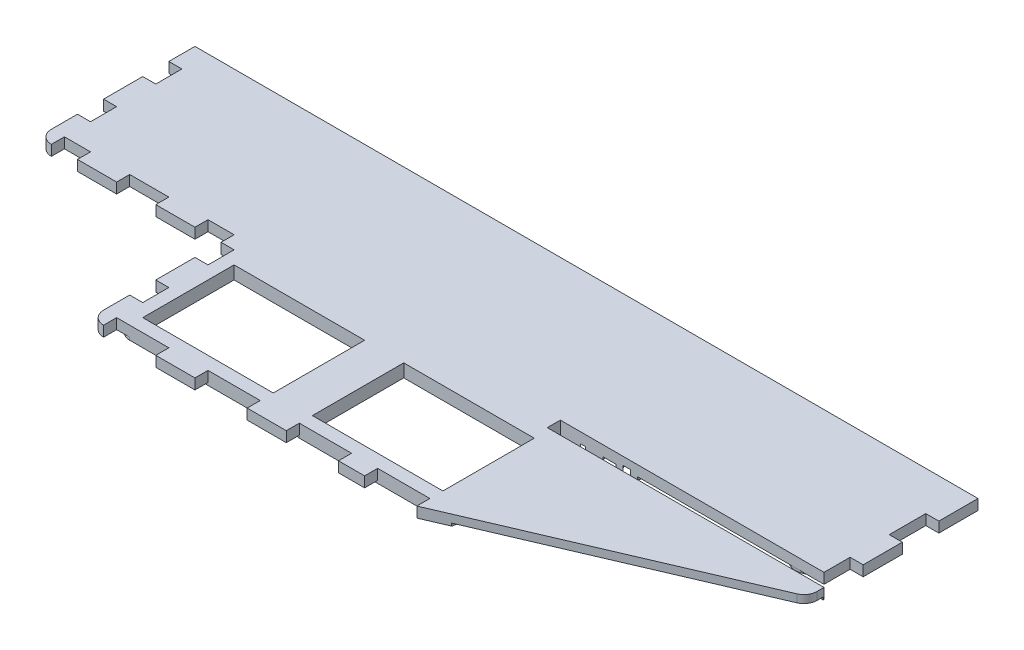
SolidWorks part; units mm, degrees
ref_plane "Front Plane" through (0, 0, 0) normal (0, 0, 1) x (1, 0, 0)
ref_plane "Top Plane" through (0, 0, 0) normal (0, 1, 0) x (1, 0, 0)
ref_plane "Right Plane" through (0, 0, 0) normal (1, 0, 0) x (0, 0, -1)
sketch "Sketch1" plane through (0, 0, 0) normal (0, 0, 1) x (1, 0, 0)
  line L0 (0, 0) -> (0, 254) construction
  line L1 (-381, 0) -> (0, 0)
  line L3 (-381, 6.35) -> (0, 6.35)
  line L4 (0, 0) -> (0, 6.35)
  line L5 (-381, 0) -> (-381, 6.35)
extrude "Boss-Extrude1" add sketch "Sketch1" along normal blind 139.7
sketch "Sketch2" plane through (0, 0, 0) normal (0, -1, 0) x (1, 0, 0)
  line L1 (-406.4, 139.7) -> (-406.4, 0) construction
  line L2 (-374.65, 76.2) -> (-292.1, 76.2)
  line L3 (-292.1, 76.2) -> (-292.1, 133.35)
  line L4 (-381, 139.7) -> (0, 139.7) construction
  line L5 (-285.75, 139.7) -> (-133.35, 139.7)
  line L6 (-133.35, 139.7) -> (-3.8486, 84.1994)
  line L7 (0, 139.7) -> (0, 0) construction
  line L8 (0, 78.3628) -> (0, 0)
  line L9 (0, 0) -> (-381, 0)
  line L10 (-381, 69.85) -> (-381, 0)
  line L11 (-381, 139.7) -> (-381, 0) construction
  arc A0 (-3.8486, 84.1994) -> (0, 78.3628) centre (-6.35, 78.3628) cw
  arc A1 (-292.1, 133.35) -> (-285.75, 139.7) centre (-285.75, 133.35) cw
  arc A3 (-381, 69.85) -> (-374.65, 76.2) centre (-374.65, 69.85) cw
  point P17 (0, 82.55)
  point P20 (-292.1, 139.7)
  point P21 (-381, 76.2)
  point P23 (-406.4, 76.2)
  dimension "D5" = 6.35
  dimension "D1" = 6.35
  dimension "D2" = 114.3
  dimension "D3" = 158.75
  dimension "D4" = 82.55
extrude "Cut-Extrude1" cut sketch "Sketch2" against normal through all
sketch "Sketch3" plane through (0, 6.35, 0) normal (0, 1, 0) x (1, 0, 0)
  line L0 (-133.35, -139.7) -> (-285.75, -139.7) construction
  line L1 (-279.4, -127) -> (-215.9, -127)
  line L2 (-279.4, -127) -> (-279.4, -82.55)
  line L3 (-279.4, -82.55) -> (-215.9, -82.55)
  line L4 (-215.9, -127) -> (-215.9, -82.55)
  line L5 (-196.85, -127) -> (-133.35, -127)
  line L6 (-196.85, -127) -> (-196.85, -82.55)
  line L7 (-196.85, -82.55) -> (-133.35, -82.55)
  line L8 (-133.35, -127) -> (-133.35, -82.55)
  line L9 (-292.1, -76.2) -> (-292.1, -133.35) construction
  dimension "D1" = 44.45
  dimension "D2" = 12.7
  dimension "D3" = 12.7
  dimension "D4" = 63.5
  dimension "D5" = 19.05
  dimension "D6" = 44.45
  dimension "D7" = 12.7
  dimension "D8" = 63.5
extrude "Cut-Extrude2" cut sketch "Sketch3" against normal through all contours L5 L8 L7 L6 | L1 L4 L3 L2
sketch "Sketch4" plane through (0, 0, 0) normal (0, -1, 0) x (1, 0, 0)
  line L0 (-285.75, 139.7) -> (-133.35, 139.7) construction
  line L1 (-279.4, 133.35) -> (-215.9, 133.35)
  line L2 (-285.75, 127) -> (-285.75, 25.4)
  line L3 (-279.4, 19.05) -> (-215.9, 19.05)
  line L4 (-209.55, 127) -> (-209.55, 25.4)
  line L5 (-127, 133.35) -> (-196.85, 133.35)
  line L7 (-131.8807, 19.05) -> (-196.85, 19.05)
  line L8 (-203.2, 127) -> (-203.2, 25.4)
  line L9 (-292.1, 76.2) -> (-292.1, 133.35) construction
  line L11 (-381, 0) -> (0, 0) construction
  line L12 (-215.9, 127) -> (-215.9, 82.55) construction
  line L13 (-127, 133.35) -> (-112.1376, 74.8789)
  line L14 (-112.1376, 74.8789) -> (-125.7444, 23.7664)
  arc A0 (-196.85, 133.35) -> (-203.2, 127) centre (-196.85, 127) ccw
  arc A1 (-215.9, 133.35) -> (-209.55, 127) centre (-215.9, 127) cw
  arc A2 (-279.4, 133.35) -> (-285.75, 127) centre (-279.4, 127) ccw
  arc A3 (-285.75, 25.4) -> (-279.4, 19.05) centre (-279.4, 25.4) ccw
  arc A4 (-215.9, 19.05) -> (-209.55, 25.4) centre (-215.9, 25.4) ccw
  arc A5 (-196.85, 19.05) -> (-203.2, 25.4) centre (-196.85, 25.4) cw
  arc A6 (-131.8807, 19.05) -> (-125.7444, 23.7664) centre (-131.8807, 25.4) ccw
  dimension "D3" = 6.35
  dimension "D1" = 6.35
  dimension "D2" = 6.35
  dimension "D4" = 6.35
  dimension "D5" = 19.05
  dimension "D6" = 6.35
  dimension "D7" = 6.35
  dimension "D8" = 19.05
extrude "Cut-Extrude3" cut sketch "Sketch4" against normal blind 1.27
sketch "Sketch5" plane through (0, 0, 0) normal (0, -1, 0) x (1, 0, 0)
  line L0 (-250.8616, 56.914) -> (-269.3149, 71.6766)
  line L1 (-248.4216, 50.9666) -> (-248.4331, 50.9773) construction
  line L3 (-267.7282, 76.2) -> (-229.317, 76.2)
  line L4 (-257.258, 53.8991) -> (-275.2733, 68.3113)
  line L5 (-184.3234, 76.2) -> (-133.6398, 76.2)
  line L6 (-196.85, 82.55) -> (-133.35, 82.55) construction
  line L9 (-142.8427, 29.9409) -> (-159.4602, 42.9343)
  line L10 (-227.2884, 29.9234) -> (-246.082, 44.9583)
  line L12 (-131.9836, 71.533) -> (-158.9921, 53.9033)
  line L15 (-124.9851, 68.5182) -> (-151.5288, 51.1918)
  line L21 (-220.0267, 32.246) -> (-239.6856, 47.9731)
  line L24 (-275.269, 33.4756) -> (-257.2515, 47.954)
  line L26 (-131.8807, 25.4) -> (-118.6989, 74.9159)
  line L28 (-131.8807, 25.4) -> (-118.6989, 74.9159)
  line L30 (-118.6989, 74.9159) -> (-131.9379, 127)
  line L37 (-269.5564, 29.9199) -> (-250.8486, 44.9531)
  line L38 (-215.9, 34.2294) -> (-215.9, 67.7374)
  line L40 (-248.5328, 50.9091) -> (-248.3486, 51.0351) construction
  line L41 (-246.095, 56.9191) -> (-227.7259, 71.6801)
  line L42 (-248.5328, 50.9091) -> (-248.5037, 50.8894) construction
  line L43 (-228.8751, 25.4) -> (-267.9653, 25.4)
  line L44 (-248.3486, 51.0351) -> (-248.5037, 50.8894) construction
  line L45 (-279.4, 66.3279) -> (-279.4, 35.4556)
  line L46 (-239.6921, 53.9182) -> (-220.031, 69.7173)
  line L47 (-133.6398, 76.2) -> (-133.372, 76.2)
  line L51 (-134.0223, 31.1049) -> (-151.793, 45)
  line L55 (-163.4215, 54.0923) -> (-185.888, 71.6591)
  line L57 (-164.1074, 50.5642) -> (-164.3654, 50.8) construction
  line L58 (-131.9379, 127) -> (-196.85, 127)
  line L59 (-171.3529, 45.8348) -> (-192.9216, 31.7558)
  line L60 (-164.3654, 50.8) -> (-164.0586, 50.5961) construction
  line L61 (-196.85, 127) -> (-196.85, 25.4)
  line L62 (-164.0586, 50.5961) -> (-164.1074, 50.5642)
  line L63 (-171.0886, 52.0266) -> (-192.7454, 68.9603)
  line L65 (-163.8896, 43.1233) -> (-183.8917, 30.067)
  line L66 (-196.85, 127) -> (-196.85, 25.4)
  line L68 (-196.85, 25.4) -> (-131.8807, 25.4)
  line L70 (-196.85, 25.4) -> (-131.8807, 25.4)
  arc A0 (-257.258, 53.8991) -> (-257.2515, 47.954) centre (-259.6381, 50.924) cw
  arc A1 (-250.8486, 44.9531) -> (-246.082, 44.9583) centre (-248.462, 41.9831) cw
  arc A2 (-239.6856, 47.9731) -> (-239.6921, 53.9182) centre (-237.3055, 50.9483) cw
  arc A3 (-250.8616, 56.914) -> (-246.095, 56.9191) centre (-248.4815, 59.8891) ccw
  arc A4 (-267.7282, 76.2) -> (-269.3149, 71.6766) centre (-267.7282, 73.66) ccw
  arc A5 (-275.2733, 68.3113) -> (-279.4, 66.3279) centre (-276.86, 66.3279) ccw
  arc A6 (-279.4, 35.4556) -> (-275.269, 33.4756) centre (-276.86, 35.4556) ccw
  arc A7 (-267.9653, 25.4) -> (-269.5564, 29.9199) centre (-267.9653, 27.94) cw
  arc A8 (-227.2884, 29.9234) -> (-228.8751, 25.4) centre (-228.8751, 27.94) cw
  arc A9 (-220.0267, 32.246) -> (-215.9, 34.2294) centre (-218.44, 34.2294) ccw
  arc A10 (-215.9, 67.7374) -> (-220.031, 69.7173) centre (-218.44, 67.7374) ccw
  arc A11 (-227.7259, 71.6801) -> (-229.317, 76.2) centre (-229.317, 73.66) ccw
  arc A12 (-183.8917, 30.067) -> (-182.5033, 25.4) centre (-182.5033, 27.94) ccw
  arc A13 (-142.8427, 29.9409) -> (-144.4073, 25.4) centre (-144.4073, 27.94) cw
  arc A14 (-124.9851, 68.5182) -> (-121.1422, 65.7378) centre (-123.5967, 66.3912) cw
  arc A15 (-133.372, 76.2) -> (-131.9836, 71.533) centre (-133.372, 73.66) cw
  arc A16 (-134.0223, 31.1049) -> (-130.0033, 32.4524) centre (-132.4578, 33.1058) ccw
  arc A17 (-192.9216, 31.7558) -> (-196.85, 33.8828) centre (-194.31, 33.8828) cw
  arc A18 (-196.85, 66.9593) -> (-192.7454, 68.9603) centre (-194.31, 66.9593) cw
  arc A19 (-185.888, 71.6591) -> (-184.3234, 76.2) centre (-184.3234, 73.66) cw
  arc A20 (-171.3529, 45.8348) -> (-171.0886, 52.0266) centre (-173.4355, 49.0252) ccw
  arc A21 (-163.8896, 43.1233) -> (-159.4602, 42.9343) centre (-161.807, 39.9329) cw
  arc A22 (-151.793, 45) -> (-151.5288, 51.1918) centre (-149.4462, 48.0014) cw
  arc A23 (-158.9921, 53.9033) -> (-163.4215, 54.0923) centre (-161.0746, 57.0937) cw
  point P13 (-247.9043, 50.4821)
  point P14 (-248.3486, 51.0351)
  point P39 (-243.3962, 50.9416)
  point P55 (-157.9377, 50.8)
  point P56 (-164.3654, 50.8)
  point P88 (-166.8929, 48.746)
  dimension "D5" = 3.81
  dimension "D1" = 2.54
  dimension "D4" = 2.54
  dimension "D6" = 2.54
  dimension "D7" = 2.54
  dimension "D8" = 3.81
  dimension "D3" = 6.35
  dimension "D2" = 6.35
extrude "Cut-Extrude4" cut sketch "Sketch5" against normal blind 1.27 contours A23 L12 A15 L47 L5 A19 L55 | A22 L51 A16 L28 A14 L15 | A21 L65 A12 L70 A13 L9 | L59 A20 L63 A18 L66 A17 | L38 A10 L46 A2 L21 A9 | A8 L10 A1 L37 A7 L43 | L41 A11 L3 A4 L0 A3 | L45 A6 L24 A0 L4 A5
sketch "Sketch6" plane through (0, 1.27, 0) normal (0, -1, 0) x (1, 0, 0)
  line L0 (-288.798, 6.985) -> (-288.798, 13.335) construction
  line L1 (-291.846, 6.985) -> (-291.846, 13.335)
  line L2 (-285.75, 6.985) -> (-285.75, 13.335)
  line L3 (-270.002, 6.985) -> (-270.002, 13.335) construction
  line L6 (-273.05, 6.985) -> (-273.05, 13.335)
  line L9 (-266.954, 6.985) -> (-266.954, 13.335)
  line L12 (-251.206, 6.985) -> (-251.206, 13.335) construction
  line L15 (-381, 0) -> (0, 0) construction
  line L17 (-254.254, 6.985) -> (-254.254, 13.335)
  line L18 (-248.158, 6.985) -> (-248.158, 13.335)
  line L19 (-162.56, 6.985) -> (-162.56, 13.335) construction
  line L20 (-165.608, 6.985) -> (-165.608, 13.335)
  line L21 (-159.512, 6.985) -> (-159.512, 13.335)
  line L22 (-143.764, 6.985) -> (-143.764, 13.335) construction
  line L23 (-146.812, 6.985) -> (-146.812, 13.335)
  line L24 (-140.716, 6.985) -> (-140.716, 13.335)
  line L25 (-124.968, 6.985) -> (-124.968, 13.335) construction
  line L26 (-128.016, 6.985) -> (-128.016, 13.335)
  line L27 (-121.92, 6.985) -> (-121.92, 13.335)
  line L28 (-381, 69.85) -> (-381, 0) construction
  arc A0 (-291.846, 6.985) -> (-285.75, 6.985) centre (-288.798, 6.985) ccw
  arc A1 (-285.75, 13.335) -> (-291.846, 13.335) centre (-288.798, 13.335) ccw
  arc A5 (-286.5205, 4.8853) -> (-286.5215, 4.9583) centre (-289.4119, 4.8853) ccw
  arc A7 (-286.5205, 4.8853) -> (-286.5215, 4.9583) centre (-289.4119, 4.8853) ccw
  arc A9 (-286.5205, 4.8853) -> (-286.5215, 4.9583) centre (-289.4119, 4.8853) ccw
  arc A10 (-273.05, 6.985) -> (-266.954, 6.985) centre (-270.002, 6.985) ccw
  arc A11 (-266.954, 13.335) -> (-273.05, 13.335) centre (-270.002, 13.335) ccw
  arc A12 (-254.254, 6.985) -> (-248.158, 6.985) centre (-251.206, 6.985) ccw
  arc A13 (-248.158, 13.335) -> (-254.254, 13.335) centre (-251.206, 13.335) ccw
  arc A14 (-165.608, 6.985) -> (-159.512, 6.985) centre (-162.56, 6.985) ccw
  arc A15 (-159.512, 13.335) -> (-165.608, 13.335) centre (-162.56, 13.335) ccw
  arc A16 (-146.812, 6.985) -> (-140.716, 6.985) centre (-143.764, 6.985) ccw
  arc A17 (-140.716, 13.335) -> (-146.812, 13.335) centre (-143.764, 13.335) ccw
  arc A18 (-128.016, 6.985) -> (-121.92, 6.985) centre (-124.968, 6.985) ccw
  arc A19 (-121.92, 13.335) -> (-128.016, 13.335) centre (-124.968, 13.335) ccw
  point P2 (-288.798, 10.16)
  point P9 (-289.4119, -1.7103)
  point P11 (-270.002, 10.16)
  point P16 (-289.4119, 0)
  point P18 (-251.206, 10.16)
  point P23 (-289.4119, 0)
  point P28 (-162.56, 10.16)
  point P30 (-289.4119, 0)
  point P41 (-143.764, 10.16)
  point P48 (-124.968, 10.16)
  point P57 (-248.158, 10.16)
  dimension "D1" = 3.048
  dimension "D2" = 6.35
  dimension "D3" = 10.16
  dimension "D4" = 95.25
  dimension "D5" = 12.7
  dimension "D6" = 12.7
  dimension "D7" = 82.55
  dimension "D8" = 12.7
  dimension "D9" = 12.7
extrude "Cut-Extrude5" cut sketch "Sketch6" against normal blind 1.27 contours L18 A13 L17 A12 | L21 A15 L20 A14 | L24 A17 L23 A16 | L27 A19 L26 A18 | L9 A11 L6 A10 | L2 A1 L1 A0
sketch "Sketch7" plane through (0, 1.27, 0) normal (0, -1, 0) x (1, 0, 0)
  ellipse E0 centre (-102.3292, 61.2539) end of major axis (-102.3292, 71.8921) minor radius 7.2651
extrude "Boss-Extrude2" add sketch "Sketch7" along normal blind 1.27
sketch "Sketch8" plane through (0, 0, 0) normal (0, -1, 0) x (1, 0, 0)
  spline S0 degree 3 poles (-102.5457, 53.1558) (-102.1128, 53.1558) (-101.9017, 53.1847) (-101.4887, 53.2926) (-101.286, 53.3725) (-100.9061, 53.5658) (-100.7263, 53.6798) (-100.3826, 53.9355) (-100.2199, 54.0767) (-99.7641, 54.523) (-99.4978, 54.8539) (-99.0202, 55.5645) (-98.8146, 55.9368) (-98.4565, 56.7025) (-98.3038, 57.0969) (-98.0439, 57.9056) (-97.9369, 58.3207) (-97.6852, 59.5649) (-97.6045, 60.4029) (-97.604, 61.6715) (-97.6245, 62.0987) (-97.7076, 62.9434) (-97.7697, 63.3607) (-98.0198, 64.5967) (-98.2685, 65.4004) (-98.8106, 66.5641) (-99.0169, 66.9375) (-99.4909, 67.6447) (-99.7614, 67.9817) (-100.2165, 68.4281) (-100.3767, 68.5675) (-100.7186, 68.8228) (-100.9015, 68.9393) (-101.2816, 69.1335) (-101.4804, 69.2125) (-101.8977, 69.3226) (-102.1082, 69.3513) (-102.5329, 69.3528) (-102.7497, 69.3244) (-103.1637, 69.2174) (-103.3649, 69.1387) (-103.748, 68.9447) (-103.9279, 68.8308) (-104.2697, 68.5773) (-104.4325, 68.4367) (-104.8923, 67.9876) (-105.1581, 67.6571) (-105.6325, 66.9527) (-105.8414, 66.5759) (-106.381, 65.423) (-106.6338, 64.6169) (-106.8884, 63.364) (-106.9508, 62.9429) (-107.0335, 62.1027) (-107.0541, 61.6823) (-107.0545, 60.8405) (-107.0345, 60.4193) (-106.9523, 59.576) (-106.8897, 59.1521) (-106.6374, 57.9049) (-106.3864, 57.0988) (-105.8458, 55.9402) (-105.6383, 55.5651) (-105.2832, 55.0361) (-105.1572, 54.8648) (-104.8873, 54.5343) (-104.7428, 54.3746) (-104.4383, 54.0765) (-104.2778, 53.9373) (-103.9365, 53.6828) (-103.7539, 53.5667) (-103.3731, 53.3727) (-103.175, 53.2943) (-102.7592, 53.185) (-102.5457, 53.1558) (-102.1128, 53.1558) (-101.9017, 53.1847) knots -0.015625 -0.015625 0 0 0.015625 0.015625 0.03125 0.03125 0.046875 0.046875 0.0625 0.0625 0.09375 0.09375 0.125 0.125 0.15625 0.15625 0.1875 0.1875 0.25 0.25 0.28125 0.28125 0.3125 0.3125 0.375 0.375 0.40625 0.40625 0.4375 0.4375 0.453125 0.453125 0.46875 0.46875 0.484375 0.484375 0.5 0.5 0.515625 0.515625 0.53125 0.53125 0.546875 0.546875 0.5625 0.5625 0.59375 0.59375 0.625 0.625 0.6875 0.6875 0.71875 0.71875 0.75 0.75 0.78125 0.78125 0.8125 0.8125 0.875 0.875 0.90625 0.90625 0.921875 0.921875 0.9375 0.9375 0.953125 0.953125 0.96875 0.96875 0.984375 0.984375 1 1 1.015625 1.015625 1.03125 only from (-102.3292, 53.1558) to (-102.3292, 53.1558)
  spline S1 degree 3 poles (-102.5457, 53.1558) (-102.1128, 53.1558) (-101.9017, 53.1847) (-101.4887, 53.2926) (-101.286, 53.3725) (-100.9061, 53.5658) (-100.7263, 53.6798) (-100.3826, 53.9355) (-100.2199, 54.0767) (-99.7641, 54.523) (-99.4978, 54.8539) (-99.0202, 55.5645) (-98.8146, 55.9368) (-98.4565, 56.7025) (-98.3038, 57.0969) (-98.0439, 57.9056) (-97.9369, 58.3207) (-97.6852, 59.5649) (-97.6045, 60.4029) (-97.604, 61.6715) (-97.6245, 62.0987) (-97.7076, 62.9434) (-97.7697, 63.3607) (-98.0198, 64.5967) (-98.2685, 65.4004) (-98.8106, 66.5641) (-99.0169, 66.9375) (-99.4909, 67.6447) (-99.7614, 67.9817) (-100.2165, 68.4281) (-100.3767, 68.5675) (-100.7186, 68.8228) (-100.9015, 68.9393) (-101.2816, 69.1335) (-101.4804, 69.2125) (-101.8977, 69.3226) (-102.1082, 69.3513) (-102.5329, 69.3528) (-102.7497, 69.3244) (-103.1637, 69.2174) (-103.3649, 69.1387) (-103.748, 68.9447) (-103.9279, 68.8308) (-104.2697, 68.5773) (-104.4325, 68.4367) (-104.8923, 67.9876) (-105.1581, 67.6571) (-105.6325, 66.9527) (-105.8414, 66.5759) (-106.381, 65.423) (-106.6338, 64.6169) (-106.8884, 63.364) (-106.9508, 62.9429) (-107.0335, 62.1027) (-107.0541, 61.6823) (-107.0545, 60.8405) (-107.0345, 60.4193) (-106.9523, 59.576) (-106.8897, 59.1521) (-106.6374, 57.9049) (-106.3864, 57.0988) (-105.8458, 55.9402) (-105.6383, 55.5651) (-105.2832, 55.0361) (-105.1572, 54.8648) (-104.8873, 54.5343) (-104.7428, 54.3746) (-104.4383, 54.0765) (-104.2778, 53.9373) (-103.9365, 53.6828) (-103.7539, 53.5667) (-103.3731, 53.3727) (-103.175, 53.2943) (-102.7592, 53.185) (-102.5457, 53.1558) (-102.1128, 53.1558) (-101.9017, 53.1847) knots -0.015625 -0.015625 0 0 0.015625 0.015625 0.03125 0.03125 0.046875 0.046875 0.0625 0.0625 0.09375 0.09375 0.125 0.125 0.15625 0.15625 0.1875 0.1875 0.25 0.25 0.28125 0.28125 0.3125 0.3125 0.375 0.375 0.40625 0.40625 0.4375 0.4375 0.453125 0.453125 0.46875 0.46875 0.484375 0.484375 0.5 0.5 0.515625 0.515625 0.53125 0.53125 0.546875 0.546875 0.5625 0.5625 0.59375 0.59375 0.625 0.625 0.6875 0.6875 0.71875 0.71875 0.75 0.75 0.78125 0.78125 0.8125 0.8125 0.875 0.875 0.90625 0.90625 0.921875 0.921875 0.9375 0.9375 0.953125 0.953125 0.96875 0.96875 0.984375 0.984375 1 1 1.015625 1.015625 1.03125 only from (-102.3292, 53.1558) to (-102.3292, 53.1558)
  dimension "D1" = 2.54
extrude "Cut-Extrude6" cut sketch "Sketch8" against normal blind 2.54
sketch "Sketch9" plane through (0, 1.27, 0) normal (0, -1, 0) x (1, 0, 0)
  circle A0 centre (-20.3877, 60.8315) radius 7.62
  dimension "D1" = 15.24
extrude "Boss-Extrude3" add sketch "Sketch9" along normal blind 1.27
sketch "Sketch10" plane through (0, 0, 0) normal (0, -1, 0) x (1, 0, 0)
  circle A2 centre (-20.3877, 60.8315) radius 5.08
  circle A3 centre (-20.3877, 60.8315) radius 5.08
  dimension "D1" = 2.54
extrude "Cut-Extrude7" cut sketch "Sketch10" against normal blind 2.54
sketch "Sketch13" plane through (0, 1.27, 0) normal (0, -1, 0) x (1, 0, 0)
  line L0 (-119.1478, 125.4549) -> (-106.4217, 75.3886)
  line L1 (-106.4217, 75.3886) -> (0, 75.3886)
  line L2 (0, 0) -> (0, 78.3628) construction
  line L3 (-119.1478, 125.4549) -> (-121.475, 134.6107)
  line L4 (-3.8486, 84.1994) -> (-133.35, 139.7) construction
  line L5 (0, 75.3886) -> (0, 78.3628)
  line L6 (-3.8486, 84.1994) -> (-121.475, 134.6107)
  arc A0 (0, 78.3628) -> (-3.8486, 84.1994) centre (-6.35, 78.3628) ccw construction
  arc A1 (0, 78.3628) -> (-3.8486, 84.1994) centre (-6.35, 78.3628) ccw
extrude "Cut-Extrude10" cut sketch "Sketch13" against normal blind 1.27 contours L5 A1 L6 L3 L0 L1
sketch "Sketch14" plane through (0, 1.27, 0) normal (0, -1, 0) x (1, 0, 0)
  line L1 (-355.6, 72.8674) -> (-344.17, 72.8674)
  line L2 (-355.6, 72.8674) -> (-355.6, 66.5174)
  line L3 (-355.6, 66.5174) -> (-344.17, 66.5174)
  line L4 (-344.17, 72.8674) -> (-344.17, 66.5174)
  line L6 (-381, 69.85) -> (-381, 0) construction
  circle A0 centre (-370.84, 62.8553) radius 5.08
  dimension "D1" = 10.16
  dimension "D5" = 10.16
  dimension "D2" = 25.4
  dimension "D3" = 6.35
  dimension "D4" = 11.43
extrude "Boss-Extrude4" add sketch "Sketch14" along normal blind 1.27
ref_plane "Plane2" through (0, 3.175, 0) normal (0, -1, 0) x (-1, 0, 0)
sketch "Sketch15" plane through (0, 1.27, 0) normal (0, -1, 0) x (1, 0, 0)
  line L0 (-374.65, 76.2) -> (-381, 76.2)
  line L2 (-292.1, 76.2) -> (-374.65, 76.2) construction
  line L3 (-381, 76.2) -> (-381, 57.15)
  line L4 (-381, 69.85) -> (-381, 0) construction
  line L5 (-381, 57.15) -> (-374.65, 57.15)
  line L6 (-374.65, 57.15) -> (-374.65, 44.45)
  line L7 (-374.65, 44.45) -> (-381, 44.45)
  line L8 (-381, 44.45) -> (-381, 25.4)
  line L9 (-381, 25.4) -> (-374.65, 25.4)
  line L10 (-374.65, 25.4) -> (-374.65, 12.7)
  line L12 (-374.65, 12.7) -> (-381, 12.7)
  line L13 (-381, 12.7) -> (-381, 0)
  line L14 (-381, 76.2) -> (-381, 0)
  dimension "D1" = 6.35
  dimension "D2" = 6.35
  dimension "D3" = 6.35
  dimension "D4" = 19.05
  dimension "D5" = 12.7
  dimension "D6" = 19.05
  dimension "D7" = 12.7
  dimension "D8" = 12.7
extrude "Cut-Extrude11" cut sketch "Sketch15" against normal blind 6.35 contours L5 L14 L7 L6 | L9 L14 L12 L10
sketch "Sketch16" plane through (0, 1.27, 0) normal (0, -1, 0) x (1, 0, 0)
  line L0 (-292.1, 76.2) -> (-374.65, 76.2) construction
  line L1 (-374.65, 76.2) -> (-361.95, 76.2)
  line L2 (-374.65, 76.2) -> (-374.65, 69.85)
  line L3 (-374.65, 69.85) -> (-361.95, 69.85)
  line L5 (-381, 69.85) -> (-381, 57.15) construction
  line L6 (-361.95, 69.85) -> (-361.95, 76.2)
  line L8 (-342.9, 76.2) -> (-342.9, 69.85)
  line L9 (-342.9, 69.85) -> (-323.85, 69.85)
  line L10 (-323.85, 69.85) -> (-323.85, 76.2)
  line L11 (-304.8, 76.2) -> (-292.1, 76.2)
  line L12 (-342.9, 69.85) -> (-323.85, 69.85)
  line L13 (-342.9, 76.2) -> (-323.85, 76.2)
  line L14 (-304.8, 76.2) -> (-304.8, 69.85)
  line L15 (-304.8, 69.85) -> (-292.1, 69.85)
  line L16 (-292.1, 76.2) -> (-292.1, 69.85)
  dimension "D1" = 6.35
  dimension "D2" = 6.35
  dimension "D3" = 19.05
  dimension "D4" = 19.05
  dimension "D5" = 12.7
  dimension "D6" = 12.7
  dimension "D7" = 19.05
extrude "Cut-Extrude12" cut sketch "Sketch16" against normal blind 6.35 contours L3 L6 L1 L2 | L13 L8 L9 L10 | L16 L11 L14 L15
sketch "Sketch17" plane through (0, 1.27, 0) normal (0, -1, 0) x (1, 0, 0)
  line L0 (-292.1, 133.35) -> (-292.1, 69.85) construction
  line L1 (-304.8, 69.85) -> (-292.1, 69.85) construction
  line L2 (-292.1, 76.2) -> (-285.75, 76.2)
  line L3 (-292.1, 76.2) -> (-292.1, 88.9)
  line L4 (-292.1, 88.9) -> (-285.75, 88.9)
  line L5 (-285.75, 76.2) -> (-285.75, 88.9)
  line L6 (-285.75, 127) -> (-285.75, 25.4) construction
  line L7 (-292.1, 107.95) -> (-285.75, 107.95)
  line L8 (-292.1, 107.95) -> (-292.1, 120.65)
  line L9 (-292.1, 120.65) -> (-285.75, 120.65)
  line L10 (-285.75, 107.95) -> (-285.75, 120.65)
  dimension "D1" = 6.35
  dimension "D2" = 6.35
  dimension "D3" = 12.7
  dimension "D4" = 19.05
  dimension "D5" = 12.7
extrude "Cut-Extrude13" cut sketch "Sketch17" against normal blind 6.35 contours L2 L5 L4 L3 | L7 L10 L9 L8
sketch "Sketch18" plane through (0, 1.27, 0) normal (0, -1, 0) x (1, 0, 0)
  line L0 (-127, 133.35) -> (-196.85, 133.35) construction
  line L1 (-158.75, 133.35) -> (-133.35, 133.35)
  line L6 (-158.75, 133.35) -> (-158.75, 139.7)
  line L15 (-158.75, 139.7) -> (-133.35, 139.7)
  line L20 (-133.35, 133.35) -> (-133.35, 139.7)
  line L21 (-133.35, 139.7) -> (-285.75, 139.7) construction
  line L22 (-285.75, 139.7) -> (-260.35, 139.7)
  line L23 (-285.75, 139.7) -> (-285.75, 133.35)
  line L24 (-285.75, 133.35) -> (-260.35, 133.35)
  line L25 (-260.35, 139.7) -> (-260.35, 133.35)
  line L26 (-292.1, 133.35) -> (-292.1, 120.65) construction
  line L27 (-241.3, 139.7) -> (-215.9, 139.7)
  line L28 (-241.3, 139.7) -> (-241.3, 133.35)
  line L29 (-241.3, 133.35) -> (-215.9, 133.35)
  line L30 (-215.9, 139.7) -> (-215.9, 133.35)
  line L31 (-196.85, 139.7) -> (-171.45, 139.7)
  line L32 (-196.85, 139.7) -> (-196.85, 133.35)
  line L33 (-196.85, 133.35) -> (-171.45, 133.35)
  line L34 (-171.45, 139.7) -> (-171.45, 133.35)
  point P20 (-260.35, 136.525)
  dimension "D1" = 6.35
  dimension "D2" = 6.35
  dimension "D3" = 25.4
  dimension "D4" = 6.35
  dimension "D5" = 25.4
  dimension "D6" = 6.35
  dimension "D7" = 25.4
  dimension "D8" = 19.05
  dimension "D9" = 25.4
  dimension "D10" = 19.05
  dimension "D11" = 12.7
extrude "Cut-Extrude14" cut sketch "Sketch18" against normal blind 6.35 contours L25 L22 L23 L24 | L30 L27 L28 L29 | L34 L31 L32 L33 | L1 L20 L15 L6
sketch "Sketch19" plane through (0, 1.27, 0) normal (0, -1, 0) x (1, 0, 0)
  line L0 (0, 0) -> (0, 75.3886) construction
  line L5 (0, 55.88) -> (-6.35, 55.88)
  line L6 (0, 55.88) -> (0, 74.93)
  line L7 (0, 74.93) -> (-6.35, 74.93)
  line L8 (-6.35, 55.88) -> (-6.35, 74.93)
  line L9 (-381, 0) -> (0, 0) construction
  line L14 (0, 19.05) -> (-6.35, 19.05)
  line L15 (0, 19.05) -> (0, 36.83)
  line L16 (0, 36.83) -> (-6.35, 36.83)
  line L17 (-6.35, 19.05) -> (-6.35, 36.83)
  dimension "D1" = 6.35
  dimension "D2" = 6.35
  dimension "D3" = 17.78
  dimension "D4" = 19.05
  dimension "D5" = 19.05
  dimension "D6" = 19.05
extrude "Cut-Extrude15" cut sketch "Sketch19" against normal blind 6.35
sketch "Sketch20" plane through (0, 6.35, 0) normal (0, 1, 0) x (1, 0, 0)
  line L1 (-6.35, -74.93) -> (-134.62, -74.93)
  line L2 (-6.35, -74.93) -> (-6.35, -68.58)
  line L3 (-6.35, -68.58) -> (-134.62, -68.58)
  line L4 (-134.62, -74.93) -> (-134.62, -68.58)
  dimension "D1" = 6.35
  dimension "D2" = 128.27
extrude "Cut-Extrude16" cut sketch "Sketch20" against normal blind 6.35
